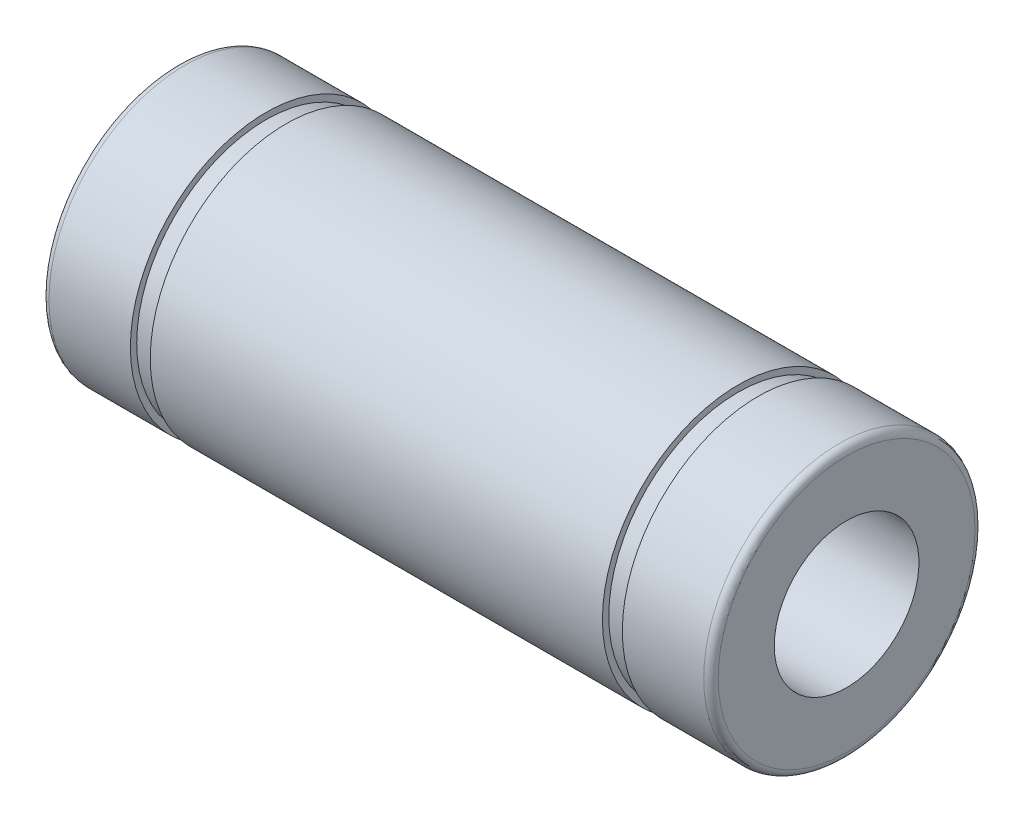
SolidWorks part; units mm, degrees
ref_plane "Front Plane" through (0, 0, 0) normal (0, 0, 1) x (1, 0, 0)
ref_plane "Top Plane" through (0, 0, 0) normal (0, 1, 0) x (1, 0, 0)
ref_plane "Right Plane" through (0, 0, 0) normal (1, 0, 0) x (0, 0, -1)
ref_plane "Plane1" through (0, 0, 0) normal (0, 0, 1) x (1, 0, 0)
sketch "Sketch1" plane through (0, 0, 0) normal (0, 0, 1) x (1, 0, 0)
  line L0 (-18.5, 7.1) -> (-18.5, 4)
  line L1 (-18.5, 4) -> (18.5, 4)
  line L2 (18.5, 4) -> (18.5, 7.1)
  line L3 (18.1, 7.5) -> (13.6, 7.5)
  line L4 (13.6, 7.5) -> (13.6, 7.15)
  line L5 (13.6, 7.15) -> (12.5, 7.15)
  line L6 (12.5, 7.15) -> (12.5, 7.5)
  line L7 (12.5, 7.5) -> (-12.5, 7.5)
  line L8 (-12.5, 7.5) -> (-12.5, 7.15)
  line L9 (-12.5, 7.15) -> (-13.6, 7.15)
  line L10 (-13.6, 7.15) -> (-13.6, 7.5)
  line L11 (-13.6, 7.5) -> (-18.1, 7.5)
  line L12 (18.5, 0) -> (-18.5, 0) construction
  line L13 (0, 7.5) -> (0, 0) construction
  line L14 (-18.5, 4) -> (-18.5, 0) construction
  arc A0 (18.5, 7.1) -> (18.1, 7.5) centre (18.1, 7.1) ccw
  arc A1 (-18.1, 7.5) -> (-18.5, 7.1) centre (-18.1, 7.1) ccw
  dimension "D7" = 0.4
  dimension "D1" = 37
  dimension "D2" = 15
  dimension "D3" = 8
  dimension "D4" = 25
  dimension "D5" = 1.1
  dimension "D6" = 14.3
revolve "Revolve1" add sketch "Sketch1" angle 360 about L12
